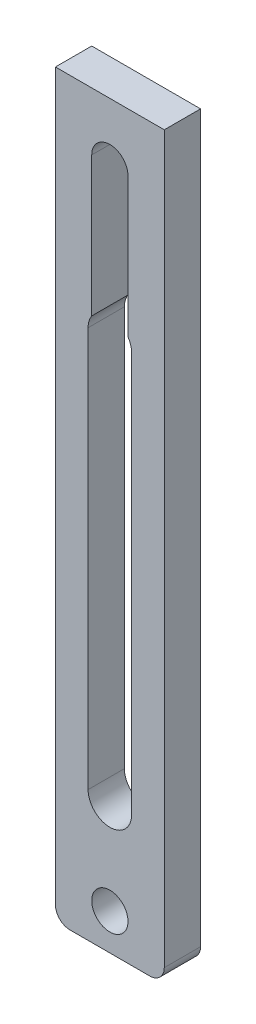
SolidWorks part; units mm, degrees
ref_plane "Front Plane" through (0, 0, 0) normal (0, 0, 1) x (1, 0, 0)
ref_plane "Top Plane" through (0, 0, 0) normal (0, 1, 0) x (1, 0, 0)
ref_plane "Right Plane" through (0, 0, 0) normal (1, 0, 0) x (0, 0, -1)
sketch "Sketch1" plane through (0, 0, 0) normal (0, 0, 1) x (1, 0, 0)
  line L1 (-6.985, -64.77) -> (6.985, -64.77)
  line L2 (-9.525, -62.23) -> (-9.525, 64.77)
  line L3 (-9.525, 64.77) -> (9.525, 64.77)
  line L4 (9.525, -62.23) -> (9.525, 64.77)
  line L5 (-9.525, -64.77) -> (9.525, 64.77) construction
  line L6 (-9.525, 64.77) -> (9.525, -64.77) construction
  circle A0 centre (0, -58.42) radius 3.175
  arc A1 (6.985, -64.77) -> (9.525, -62.23) centre (6.985, -62.23) ccw
  arc A2 (-6.985, -64.77) -> (-9.525, -62.23) centre (-6.985, -62.23) cw
  point P0 (0, 0)
  dimension "D1" = 6.35
  dimension "D3" = 2.54
  dimension "D2" = 19.05
  dimension "D4" = 6.35
  dimension "D5" = 127
extrude "Boss-Extrude1" add sketch "Sketch1" along normal blind 6.35
sketch "Sketch2" plane through (0, 0, 6.35) normal (0, 0, 1) x (1, 0, 0)
  line L0 (-6.985, -64.77) -> (6.985, -64.77) construction
  line L4 (0, -41.91) -> (0, 54.61) construction
  line L5 (-3.175, -41.91) -> (-3.175, 54.61)
  line L6 (3.175, -41.91) -> (3.175, 54.61)
  line L7 (9.525, 64.77) -> (-9.525, 64.77) construction
  arc A2 (-3.175, -41.91) -> (3.175, -41.91) centre (0, -41.91) ccw
  arc A3 (3.175, 54.61) -> (-3.175, 54.61) centre (0, 54.61) ccw
  point P4 (0, -64.77)
  point P12 (0, 6.35)
  dimension "D4" = 6.35
  dimension "D5" = 10.16
  dimension "D6" = 106.68
extrude "Cut-Extrude1" cut sketch "Sketch2" against normal through all both
sketch "Sketch3" plane through (0, 0, 6.35) normal (0, 0, 1) x (1, 0, 0)
  line L0 (0, 28.0981) -> (0, -41.91) construction
  line L1 (3.81, 28.0981) -> (3.81, -41.91)
  line L2 (-3.81, 28.0981) -> (-3.81, -41.91)
  arc A0 (3.81, 28.0981) -> (-3.81, 28.0981) centre (0, 28.0981) ccw
  arc A1 (-3.81, -41.91) -> (3.81, -41.91) centre (0, -41.91) ccw
  point P3 (0, -6.9059)
  dimension "D1" = 7.62
extrude "Cut-Extrude2" cut sketch "Sketch3" against normal through all
